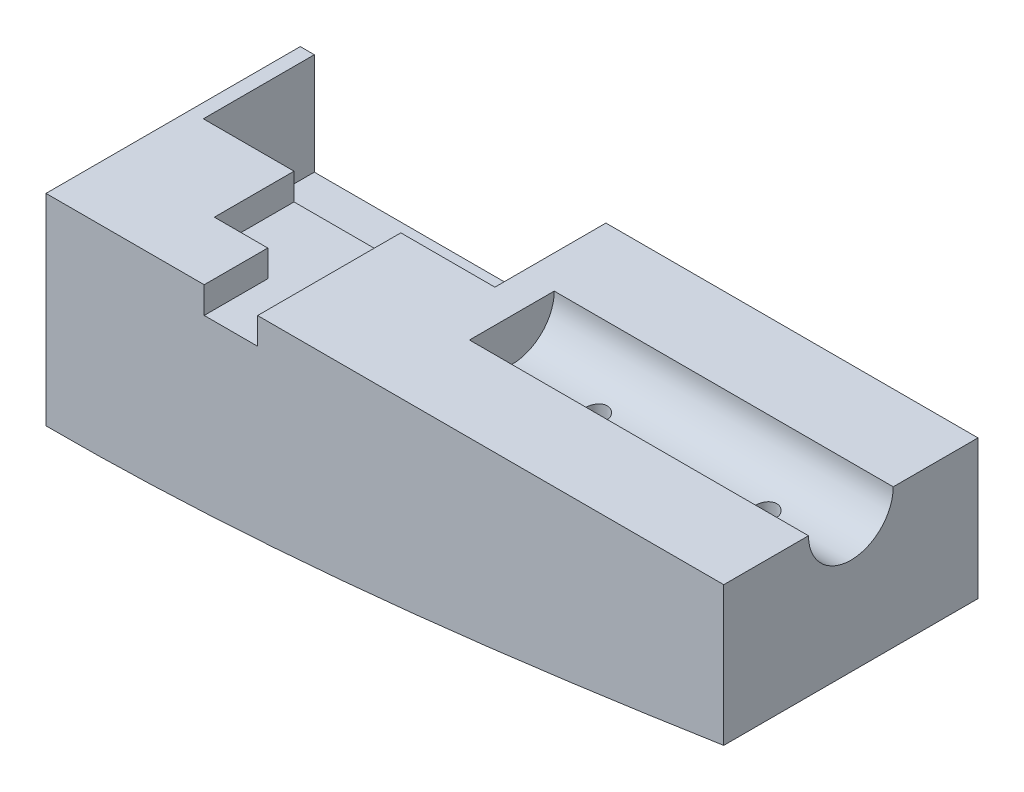
SolidWorks part; units mm, degrees
material "ABS"
ref_plane "Front Plane" through (0, 0, 0) normal (0, 0, 1) x (1, 0, 0)
ref_plane "Top Plane" through (0, 0, 0) normal (0, 1, 0) x (1, 0, 0)
ref_plane "Right Plane" through (0, 0, 0) normal (1, 0, 0) x (0, 0, -1)
curve "Curve4"
  spline degree 3 poles (100, 0, 0) (99.8498, 0.0023, 0) (99.4759, 0.008, 0) (99.1023, 0.0238, 0) (98.8789, 0.0332, 0) knots 0 0 0 0 0.401829 1 1 1 1
curve "Curve5"
  spline degree 3 poles (99.3714, -0.0082, 0) (100.2526, 0, 0) (99.3714, 0.0082, 0) (98.8504, 0.035, 0) (97.904, 0.0811, 0) (96.8285, 0.1543, 0) (95.5159, 0.2583, 0) (94.013, 0.3972, 0) (92.313, 0.574, 0) (90.4281, 0.791, 0) (88.3655, 1.0495, 0) (86.1348, 1.3497, 0) (83.7456, 1.691, 0) (81.2082, 2.0715, 0) (78.5335, 2.4886, 0) (75.7326, 2.9386, 0) (72.8172, 3.4168, 0) (69.799, 3.9177, 0) (66.6904, 4.435, 0) (63.5039, 4.9616, 0) (60.2521, 5.4899, 0) (56.948, 6.0119, 0) (53.6049, 6.519, 0) (50.2363, 7.0024, 0) (46.8558, 7.4534, 0) (43.4774, 7.8632, 0) (40.1152, 8.2232, 0) (36.7837, 8.5249, 0) (33.4975, 8.7606, 0) (30.2716, 8.923, 0) (27.1211, 9.0055, 0) (24.0614, 9.0025, 0) (21.108, 8.909, 0) (18.277, 8.7213, 0) (15.5843, 8.4369, 0) (13.0466, 8.0543, 0) (10.6806, 7.5735, 0) (8.5039, 6.996, 0) (6.5349, 6.3253, 0) (4.7933, 5.5673, 0) (3.3001, 4.7321, 0) (2.0777, 3.8366, 0) (1.1467, 2.91, 0) (0.5165, 2.0014, 0) (0.165, 1.1816, 0) (0.0231, 0.524, 0) (-0.0093, 0, 0) (0.0231, -0.524, 0) (0.165, -1.1816, 0) (0.5165, -2.0014, 0) (1.1467, -2.91, 0) (2.0777, -3.8366, 0) (3.3001, -4.7321, 0) (4.7933, -5.5673, 0) (6.5349, -6.3253, 0) (8.5039, -6.996, 0) (10.6806, -7.5735, 0) (13.0466, -8.0543, 0) (15.5843, -8.4369, 0) (18.277, -8.7213, 0) (21.108, -8.909, 0) (24.0614, -9.0025, 0) (27.1211, -9.0055, 0) (30.2716, -8.923, 0) (33.4975, -8.7606, 0) (36.7837, -8.5249, 0) (40.1152, -8.2232, 0) (43.4774, -7.8632, 0) (46.8558, -7.4534, 0) (50.2363, -7.0024, 0) (53.6049, -6.519, 0) (56.948, -6.0119, 0) (60.2521, -5.4899, 0) (63.5039, -4.9616, 0) (66.6904, -4.435, 0) (69.799, -3.9177, 0) (72.8172, -3.4168, 0) (75.7326, -2.9386, 0) (78.5335, -2.4886, 0) (81.2082, -2.0715, 0) (83.7456, -1.691, 0) (86.1348, -1.3497, 0) (88.3655, -1.0495, 0) (90.4281, -0.791, 0) (92.313, -0.574, 0) (94.013, -0.3972, 0) (95.5159, -0.2583, 0) (96.8285, -0.1543, 0) (97.904, -0.0811, 0) (98.8504, -0.035, 0) (99.3714, -0.0082, 0) (100.2526, 0, 0) (99.3714, 0.0082, 0) knots -0.009667 -0.005395 -0.002168 0 0.002168 0.005395 0.009667 0.014967 0.021271 0.028553 0.036781 0.04592 0.055932 0.066773 0.078397 0.090755 0.103793 0.117456 0.131686 0.146422 0.1616 0.177156 0.193024 0.209135 0.225421 0.241812 0.258238 0.274629 0.290914 0.307025 0.322893 0.338448 0.353626 0.368361 0.38259 0.396253 0.40929 0.421647 0.43327 0.444109 0.454119 0.463255 0.471479 0.478755 0.485052 0.490344 0.49461 0.497833 0.5 0.502167 0.50539 0.509656 0.514948 0.521245 0.528521 0.536745 0.545881 0.555891 0.56673 0.578353 0.59071 0.603747 0.61741 0.631639 0.646374 0.661552 0.677107 0.692975 0.709086 0.725371 0.741762 0.758188 0.774579 0.790865 0.806976 0.822844 0.8384 0.853578 0.868314 0.882544 0.896207 0.909245 0.921603 0.933227 0.944068 0.95408 0.963219 0.971447 0.978729 0.985033 0.990333 0.994605 0.997832 1 1.002168 1.005395 1.009667 periodic
sketch "Sketch2" plane through (0, 0, 0) normal (0, 0, 1) x (1, 0, 0)
  line L0 (2241.12, 0) -> (670.56, 0) construction
  line L1 (3.3078, -1000) -> (3.3078, 49000) construction
  line L2 (474.1307, 0) -> (0, 0) construction
  line L3 (474.1307, 25.261) -> (474.1307, -25.261)
  circle A0 centre (104.5357, 0) radius 12.7
  arc A1 (3.3078, -12.6626) -> (3.3078, 12.6626) centre (25.8906, 0) cw
  circle A2 centre (25.8906, 0) radius 25.8906
  circle A3 centre (104.5357, 0) radius 12.7
  spline S2 degree 3 poles (474.1307, 25.261) (472.1696, 25.5865) (463.25, 27.0682) (447.1994, 29.739) (425.8316, 33.2703) (404.0263, 36.8132) (381.8707, 40.3133) (359.4533, 43.7135) (336.8645, 46.9554) (314.1962, 49.9798) (291.5418, 52.7277) (268.9963, 55.1412) (246.6566, 57.1646) (224.6209, 58.7452) (202.9892, 59.8341) (181.8631, 60.3875) (161.3458, 60.367) (141.542, 59.7399) (122.5581, 58.4818) (104.5023, 56.5743) (87.485, 54.0089) (71.6197, 50.7848) (57.0237, 46.9125) (43.8205, 42.415) (32.1416, 37.3322) (22.1291, 31.7315) (13.9324, 25.7264) (7.6896, 19.5132) (3.4631, 13.4204) (1.1063, 7.9234) (0.1546, 3.5138) (-0.0622, 0) (0.1546, -3.5138) (1.1063, -7.9234) (3.4631, -13.4204) (7.6896, -19.5132) (13.9324, -25.7264) (22.1291, -31.7315) (32.1416, -37.3322) (43.8205, -42.415) (57.0237, -46.9125) (71.6197, -50.7848) (87.485, -54.0089) (104.5023, -56.5743) (122.5581, -58.4818) (141.542, -59.7399) (161.3458, -60.367) (181.8631, -60.3875) (202.9892, -59.8341) (224.6209, -58.7452) (246.6566, -57.1646) (268.9963, -55.1412) (291.5418, -52.7277) (314.1962, -49.9798) (336.8645, -46.9554) (359.4533, -43.7135) (381.8707, -40.3133) (404.0263, -36.8132) (425.8316, -33.2703) (447.1994, -29.739) (463.25, -27.0682) (472.1696, -25.5865) (474.1307, -25.261) knots 0.142144 0.142144 0.142144 0.142144 0.146422 0.1616 0.177156 0.193024 0.209135 0.225421 0.241812 0.258238 0.274629 0.290914 0.307025 0.322893 0.338448 0.353626 0.368361 0.38259 0.396253 0.40929 0.421647 0.43327 0.444109 0.454119 0.463255 0.471479 0.478755 0.485052 0.490344 0.49461 0.497833 0.5 0.502167 0.50539 0.509656 0.514948 0.521245 0.528521 0.536745 0.545881 0.555891 0.56673 0.578353 0.59071 0.603747 0.61741 0.631639 0.646374 0.661552 0.677107 0.692975 0.709086 0.725371 0.741762 0.758188 0.774579 0.790865 0.806976 0.822844 0.8384 0.853578 0.857856 0.857856 0.857856 0.857856
  point P2 (167.64, 0)
  point P8 (3.3078, -12.6626)
  point P10 (3.3078, 12.6626)
  point P21 (104.5357, 0)
  dimension "D2" = 25.4
  dimension "D1" = 167.64
extrude "Boss-Extrude1" add sketch "Sketch2" against normal blind 76.2 contours S2 L3
sketch "Sketch4" plane through (0, 0, -76.2) normal (0, 0, -1) x (-1, 0, 0)
  line L0 (0, 0) -> (-474.1307, 0) construction
  line L1 (-474.1307, 25.261) -> (-474.1307, -25.261) construction
  line L3 (-474.1307, 0) -> (0, 0)
  line L4 (-474.1307, 0) -> (-474.1307, 68.8171)
  line L5 (-474.1307, 68.8171) -> (0, 68.8171)
  line L6 (0, 0) -> (0, 68.8171)
  point P0 (0, 0)
extrude "Cut-Extrude2" cut sketch "Sketch4" against normal blind 101.6
sketch "Sketch6" plane through (0, 0, -76.2) normal (0, 0, -1) x (-1, 0, 0)
  line L0 (-474.1307, 0) -> (0, 0) construction
  circle A0 centre (-104.648, 0) radius 25.4
  dimension "D2" = 50.8
  dimension "D1" = 104.648
extrude "Cut-Extrude3" cut sketch "Sketch6" against normal through all contours A0
sketch "Sketch9" plane through (474.1307, 0, 0) normal (1, 0, 0) x (0, 0, -1)
  line L1 (-93.0865, 65.5633) -> (93.0865, 65.5633)
  line L2 (-93.0865, 65.5633) -> (-93.0865, -65.5633)
  line L3 (-93.0865, -65.5633) -> (93.0865, -65.5633)
  line L4 (93.0865, 65.5633) -> (93.0865, -65.5633)
  line L5 (-93.0865, 65.5633) -> (93.0865, -65.5633) construction
  line L6 (-93.0865, -65.5633) -> (93.0865, 65.5633) construction
  point P0 (0, 0)
extrude "Cut-Extrude4" cut sketch "Sketch9" against normal blind 101.6
sketch "Sketch10" plane through (372.5307, 0, 0) normal (1, 0, 0) x (0, 0, -1)
  line L0 (76.2, 0) -> (0, 0) construction
  circle A0 centre (38.1, 0) radius 12.7
  dimension "D1" = 25.4
extrude "Cut-Extrude5" cut sketch "Sketch10" against normal blind 101.6
sketch "Sketch12" plane through (0, 0, 0) normal (0, 1, 0) x (1, 0, 0)
  line L3 (270.9307, 50.8) -> (372.5307, 50.8) construction
  line L4 (296.3307, 38.1) -> (296.3307, 50.8) construction
  line L5 (296.3307, 38.1) -> (296.3307, 25.4) construction
  line L6 (372.5307, 25.4) -> (270.9307, 25.4) construction
  line L7 (347.1307, 38.1) -> (347.1307, 50.8) construction
  line L8 (347.1307, 38.1) -> (347.1307, 25.4) construction
  line L9 (270.9307, 25.4) -> (270.9307, 50.8) construction
  circle A0 centre (296.3307, 38.1) radius 3.175
  circle A1 centre (347.1307, 38.1) radius 3.175
  dimension "D1" = 25.4
  dimension "D2" = 76.2
  dimension "D3" = 6.35
  dimension "D4" = 6.35
extrude "Cut-Extrude7" cut sketch "Sketch12" against normal blind 101.6
sketch "Sketch14" plane through (0, 0, 0) normal (0, 1, 0) x (1, 0, 0)
  line L1 (200.8267, 19.05) -> (232.8307, 19.05)
  line L2 (200.8267, 19.05) -> (200.8267, 69.088)
  line L3 (200.8267, 69.088) -> (232.8307, 69.088)
  line L4 (232.8307, 19.05) -> (232.8307, 69.088)
  line L5 (200.8267, 19.05) -> (232.8307, 69.088) construction
  line L6 (200.8267, 69.088) -> (232.8307, 19.05) construction
  line L7 (130.048, 0) -> (372.5307, 0) construction
  line L9 (270.9307, 50.8) -> (270.9307, 25.4) construction
  line L10 (372.5307, 76.2) -> (130.048, 76.2) construction
  dimension "D1" = 32.004
  dimension "D2" = 19.05
  dimension "D3" = 7.112
  dimension "D4" = 38.1
extrude "Cut-Extrude8" cut sketch "Sketch14" against normal blind 7.9756
scale "Scale1" scale about centroid uniform scaling yes scale factor 0.5
ref_plane "Plane5" through (0, 0, -38.0725) normal (0, 0, -1) x (-1, 0, 0)
scale "Scale2" scale about centroid uniform scaling yes scale factor 2
sketch "Sketch24" plane through (0, 0, 0) normal (0, 1, 0) x (1, 0, 0)
  line L0 (372.5307, 76.2) -> (130.048, 76.2) construction
  line L1 (261.0168, 76.2) -> (173.6408, 76.2)
  line L2 (261.0168, 76.2) -> (261.0168, 42.926)
  line L3 (261.0168, 42.926) -> (173.6408, 42.926)
  line L4 (173.6408, 76.2) -> (173.6408, 42.926)
  line L5 (200.8267, 19.05) -> (232.8307, 19.05) construction
  dimension "D1" = 87.376
  dimension "D2" = 23.876
extrude "Cut-Extrude19" cut sketch "Sketch24" against normal blind 30.48
sketch "Sketch25" plane through (0, 0, -19.05) normal (0, 0, -1) x (-1, 0, 0)
  line L0 (-200.8267, 0) -> (-232.8307, 0) construction
  line L1 (-232.8307, -7.9756) -> (-216.8287, -7.9756)
  line L2 (-232.8307, -7.9756) -> (-232.8307, 0)
  line L3 (-232.8307, 0) -> (-216.8287, 0)
  line L4 (-216.8287, -7.9756) -> (-216.8287, 0)
  dimension "D1" = 16.002
extrude "Cut-Extrude20" cut sketch "Sketch25" against normal through all
sketch "Sketch26" plane through (0, 0, 0) normal (0, 1, 0) x (1, 0, 0)
  line L1 (50.8, 41.529) -> (31.75, 41.529)
  line L2 (50.8, 41.529) -> (50.8, 34.671)
  line L3 (50.8, 34.671) -> (31.75, 34.671)
  line L4 (31.75, 41.529) -> (31.75, 34.671)
  line L5 (0, 0) -> (0, 76.2) construction
  line L6 (0, 38.1) -> (98.9528, 38.1) construction
  point P10 (31.75, 38.1)
  dimension "D1" = 19.05
  dimension "D2" = 6.858
  dimension "D3" = 31.75
extrude "Cut-Extrude21" cut sketch "Sketch26" against normal blind 30.48
sketch "Sketch27" plane through (31.75, 0, 0) normal (1, 0, 0) x (0, 0, -1)
  line L1 (34.671, 0) -> (41.529, 0)
  line L2 (34.671, 0) -> (34.671, -19.05)
  line L3 (34.671, -19.05) -> (41.529, -19.05)
  line L4 (41.529, 0) -> (41.529, -19.05)
  dimension "D1" = 19.05
  dimension "D2" = 6.858
extrude "Cut-Extrude22" cut sketch "Sketch27" against normal through all
sketch "Sketch28" plane through (0, 0, 0) normal (0, 1, 0) x (1, 0, 0)
  line L0 (0, 41.529) -> (0, 76.2) construction
  line L1 (79.248, 76.2) -> (0, 76.2) construction
  line L2 (173.6408, 76.2) -> (130.048, 76.2) construction
  circle A0 centre (64.77, 38.1) radius 12.7
  circle A1 centre (152.4, 38.1) radius 12.7
  dimension "D1" = 25.4
  dimension "D2" = 25.4
  dimension "D3" = 152.4
  dimension "D4" = 64.77
  dimension "D5" = 38.1
  dimension "D6" = 38.1
extrude "Cut-Extrude23" cut sketch "Sketch28" against normal blind 12.7
sketch "Sketch29" plane through (0, 0, 0) normal (1, 0, 0) x (0, 0, -1)
  line L1 (102.719, 22.4383) -> (-23.7213, 22.4383)
  line L2 (102.719, 22.4383) -> (102.719, -79.3588)
  line L3 (102.719, -79.3588) -> (-23.7213, -79.3588)
  line L4 (-23.7213, 22.4383) -> (-23.7213, -79.3588)
  line L5 (102.719, 22.4383) -> (-23.7213, -79.3588) construction
  line L6 (102.719, -79.3588) -> (-23.7213, 22.4383) construction
  point P0 (39.4989, -28.4603)
extrude "Cut-Extrude24" cut sketch "Sketch29" along normal blind 169.418
sketch "Sketch30" plane through (169.418, 0, 0) normal (-1, 0, 0) x (0, 0, 1)
  line L0 (0, -30.1732) -> (-76.2, -30.1732) construction
  line L1 (0, 0) -> (0, -60.3464) construction
  line L2 (-76.2, 0) -> (-76.2, -60.3464) construction
  circle A0 centre (-38.1, -30.1732) radius 12.954
  dimension "D1" = 25.908
extrude "Cut-Extrude25" cut sketch "Sketch30" against normal blind 6.35
